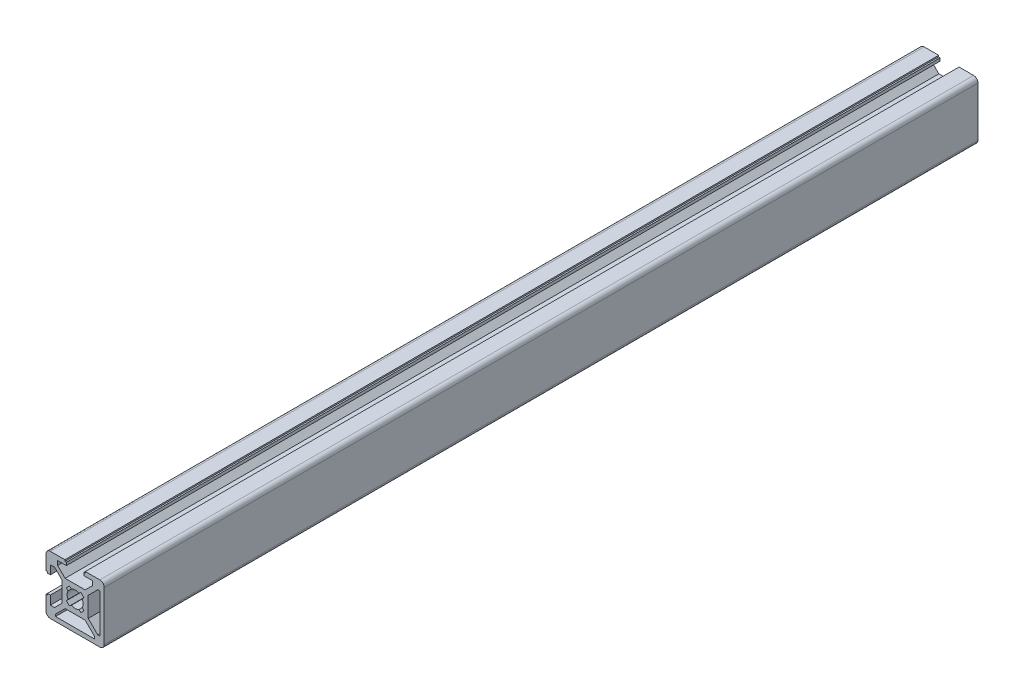
SolidWorks part; units mm, degrees
ref_plane "Front Plane" through (0, 0, 0) normal (0, 0, 1) x (1, 0, 0)
ref_plane "Top Plane" through (0, 0, 0) normal (0, 1, 0) x (1, 0, 0)
ref_plane "Right Plane" through (0, 0, 0) normal (1, 0, 0) x (0, 0, -1)
sketch "Sketch1" plane through (0, 0, 0) normal (0, 0, 1) x (1, 0, 0)
  line L1 (4.5, -3.4393) -> (4.5, 3.4393)
  line L7 (8.5, -6.7322) -> (7.7929, -6.7322)
  line L8 (7.7929, -6.7322) -> (4.5, -3.4393)
  line L9 (8.5, 6.7322) -> (8.5, -6.7322)
  line L10 (7.7929, 6.7322) -> (8.5, 6.7322)
  line L11 (4.5, 3.4393) -> (7.7929, 6.7322)
  line L21 (-2.4356, 1.2768) -> (-3.0002, 1.9496)
  line L22 (-3.0002, 1.9496) -> (-1.9496, 3.0002)
  line L23 (-1.9496, 3.0002) -> (-1.2768, 2.4356)
  line L24 (1.2768, 2.4356) -> (1.9496, 3.0002)
  line L25 (1.9496, 3.0002) -> (3.0002, 1.9496)
  line L26 (3.0002, 1.9496) -> (2.4356, 1.2768)
  line L64 (6, 7.0607) -> (3.4393, 4.5)
  line L65 (3.4393, 4.5) -> (-3.4393, 4.5)
  line L66 (-3.4393, 4.5) -> (-6, 7.0607)
  line L67 (-6, 7.0607) -> (-6, 8.5)
  line L68 (-6, 8.5) -> (-3, 8.5)
  line L69 (-3, 8.5) -> (-3, 9.5)
  line L70 (-3, 9.5) -> (-3.5, 9.5)
  line L71 (-3.5, 9.5) -> (-3.5, 10)
  line L72 (-3.5, 10) -> (-8.5, 10)
  line L73 (-10, 8.5) -> (-10, 3.5)
  line L74 (-10, 3.5) -> (-9.5, 3.5)
  line L75 (-9.5, 3.5) -> (-9.5, 3)
  line L76 (-9.5, 3) -> (-8.5, 3)
  line L77 (-8.5, 3) -> (-8.5, 6)
  line L78 (-8.5, 6) -> (-7.0607, 6)
  line L79 (-7.0607, 6) -> (-4.5, 3.4393)
  line L80 (-4.5, 3.4393) -> (-4.5, -3.4393)
  line L81 (-4.5, -3.4393) -> (-7.0607, -6)
  line L82 (-7.0607, -6) -> (-8.5, -6)
  line L83 (-8.5, -6) -> (-8.5, -3)
  line L84 (-8.5, -3) -> (-9.5, -3)
  line L85 (-9.5, -3) -> (-9.5, -3.5)
  line L86 (-9.5, -3.5) -> (-10, -3.5)
  line L87 (-10, -3.5) -> (-10, -8.5)
  line L88 (-8.5, -10) -> (8.5, -10)
  line L89 (10, -8.5) -> (10, 8.5)
  line L90 (8.5, 10) -> (3.5, 10)
  line L91 (3.5, 10) -> (3.5, 9.5)
  line L92 (3.5, 9.5) -> (3, 9.5)
  line L93 (3, 9.5) -> (3, 8.5)
  line L94 (3, 8.5) -> (6, 8.5)
  line L95 (6, 8.5) -> (6, 7.0607)
  line L97 (-1.9496, -3.0002) -> (-3.0002, -1.9496)
  line L98 (-1.2768, -2.4356) -> (-1.9496, -3.0002)
  line L99 (-3.0002, -1.9496) -> (-2.4356, -1.2768)
  line L100 (3.0002, -1.9496) -> (1.9496, -3.0002)
  line L101 (1.9496, -3.0002) -> (1.2768, -2.4356)
  line L102 (2.4356, -1.2768) -> (3.0002, -1.9496)
  line L109 (3.4393, -4.5) -> (6.7322, -7.7929)
  line L110 (6.7322, -7.7929) -> (6.7322, -8.5)
  line L111 (6.7322, -8.5) -> (-6.7322, -8.5)
  line L112 (-6.7322, -8.5) -> (-6.7322, -7.7929)
  line L113 (-3.4393, -4.5) -> (3.4393, -4.5)
  line L114 (-6.7322, -7.7929) -> (-3.4393, -4.5)
  arc A3 (1.2768, 2.4356) -> (-1.2768, 2.4356) centre (0, 0) ccw
  arc A8 (-8.5, 10) -> (-10, 8.5) centre (-8.5, 8.5) ccw
  arc A9 (-10, -8.5) -> (-8.5, -10) centre (-8.5, -8.5) ccw
  arc A10 (8.5, -10) -> (10, -8.5) centre (8.5, -8.5) ccw
  arc A11 (10, 8.5) -> (8.5, 10) centre (8.5, 8.5) ccw
  arc A15 (-1.2768, -2.4356) -> (1.2768, -2.4356) centre (0, 0) ccw
  arc A16 (2.4356, -1.2768) -> (2.4356, 1.2768) centre (0, 0) ccw
  arc A17 (-2.4356, 1.2768) -> (-2.4356, -1.2768) centre (0, 0) ccw
extrude "Boss-Extrude1" add sketch "Sketch1" along normal blind 1000
sketch "Sketch3" plane through (0, 0, 1000) normal (0, 0, 1) x (1, 0, 0)
  line L32 (6, 8.5) -> (6, 7.0607)
  line L33 (6, 7.0607) -> (3.4393, 4.5)
  line L34 (3.4393, 4.5) -> (-3.4393, 4.5)
  line L35 (-3.4393, 4.5) -> (-6, 7.0607)
  line L36 (-6, 7.0607) -> (-6, 8.5)
  line L37 (-6, 8.5) -> (-3, 8.5)
  line L38 (-3, 8.5) -> (-3, 9.5)
  line L39 (-3, 9.5) -> (-3.5, 9.5)
  line L40 (-3.5, 9.5) -> (-3.5, 10)
  line L41 (-3.5, 10) -> (-8.5, 10)
  line L42 (-10, 8.5) -> (-10, 3.5)
  line L43 (-10, 3.5) -> (-9.5, 3.5)
  line L44 (-9.5, 3.5) -> (-9.5, 3)
  line L45 (-9.5, 3) -> (-8.5, 3)
  line L46 (-8.5, 3) -> (-8.5, 6)
  line L47 (-8.5, 6) -> (-7.0607, 6)
  line L48 (-7.0607, 6) -> (-4.5, 3.4393)
  line L49 (-4.5, 3.4393) -> (-4.5, -3.4393)
  line L50 (-4.5, -3.4393) -> (-7.0607, -6)
  line L51 (-7.0607, -6) -> (-8.5, -6)
  line L52 (-8.5, -6) -> (-8.5, -3)
  line L53 (-8.5, -3) -> (-9.5, -3)
  line L54 (-9.5, -3) -> (-9.5, -3.5)
  line L55 (-9.5, -3.5) -> (-10, -3.5)
  line L56 (-10, -3.5) -> (-10, -8.5)
  line L57 (-8.5, -10) -> (8.5, -10)
  line L58 (10, -8.5) -> (10, 8.5)
  line L59 (8.5, 10) -> (3.5, 10)
  line L60 (3.5, 10) -> (3.5, 9.5)
  line L61 (3.5, 9.5) -> (3, 9.5)
  line L62 (3, 9.5) -> (3, 8.5)
  line L63 (3, 8.5) -> (6, 8.5)
  line L64 (6, 8.5) -> (6, 7.0607)
  line L65 (6, 7.0607) -> (3.4393, 4.5)
  line L66 (3.4393, 4.5) -> (-3.4393, 4.5)
  line L67 (-3.4393, 4.5) -> (-6, 7.0607)
  line L68 (-6, 7.0607) -> (-6, 8.5)
  line L69 (-6, 8.5) -> (-3, 8.5)
  line L70 (-3, 8.5) -> (-3, 9.5)
  line L71 (-3, 9.5) -> (-3.5, 9.5)
  line L72 (-3.5, 9.5) -> (-3.5, 10)
  line L73 (-3.5, 10) -> (-8.5, 10)
  line L74 (-10, 8.5) -> (-10, 3.5)
  line L75 (-10, 3.5) -> (-9.5, 3.5)
  line L76 (-9.5, 3.5) -> (-9.5, 3)
  line L77 (-9.5, 3) -> (-8.5, 3)
  line L78 (-8.5, 3) -> (-8.5, 6)
  line L79 (-8.5, 6) -> (-7.0607, 6)
  line L80 (-7.0607, 6) -> (-4.5, 3.4393)
  line L81 (-4.5, 3.4393) -> (-4.5, -3.4393)
  line L82 (-4.5, -3.4393) -> (-7.0607, -6)
  line L83 (-7.0607, -6) -> (-8.5, -6)
  line L84 (-8.5, -6) -> (-8.5, -3)
  line L85 (-8.5, -3) -> (-9.5, -3)
  line L86 (-9.5, -3) -> (-9.5, -3.5)
  line L87 (-9.5, -3.5) -> (-10, -3.5)
  line L88 (-10, -3.5) -> (-10, -8.5)
  line L89 (-8.5, -10) -> (8.5, -10)
  line L90 (10, -8.5) -> (10, 8.5)
  line L91 (8.5, 10) -> (3.5, 10)
  line L92 (3.5, 10) -> (3.5, 9.5)
  line L93 (3.5, 9.5) -> (3, 9.5)
  line L94 (3, 9.5) -> (3, 8.5)
  line L95 (3, 8.5) -> (6, 8.5)
  arc A4 (-8.5, 10) -> (-10, 8.5) centre (-8.5, 8.5) ccw
  arc A5 (-10, -8.5) -> (-8.5, -10) centre (-8.5, -8.5) ccw
  arc A6 (8.5, -10) -> (10, -8.5) centre (8.5, -8.5) ccw
  arc A7 (10, 8.5) -> (8.5, 10) centre (8.5, 8.5) ccw
  arc A8 (-8.5, 10) -> (-10, 8.5) centre (-8.5, 8.5) ccw
  arc A9 (-10, -8.5) -> (-8.5, -10) centre (-8.5, -8.5) ccw
  arc A10 (8.5, -10) -> (10, -8.5) centre (8.5, -8.5) ccw
  arc A11 (10, 8.5) -> (8.5, 10) centre (8.5, 8.5) ccw
  dimension "D1" = 0
extrude "Cut-Extrude1" cut sketch "Sketch3" against normal offset from surface (700 mm away) 300 up to face at (0, 0, 0)
sketch "Sketch4" [suppressed] plane through (0, 0, 1000) normal (0, 0, 1) x (1, 0, 0)
  line L32 (6, 8.5) -> (6, 7.0607)
  line L33 (6, 7.0607) -> (3.4393, 4.5)
  line L34 (3.4393, 4.5) -> (-3.4393, 4.5)
  line L35 (-3.4393, 4.5) -> (-6, 7.0607)
  line L36 (-6, 7.0607) -> (-6, 8.5)
  line L37 (-6, 8.5) -> (-3, 8.5)
  line L38 (-3, 8.5) -> (-3, 9.5)
  line L39 (-3, 9.5) -> (-3.5, 9.5)
  line L40 (-3.5, 9.5) -> (-3.5, 10)
  line L41 (-3.5, 10) -> (-8.5, 10)
  line L42 (-10, 8.5) -> (-10, 3.5)
  line L43 (-10, 3.5) -> (-9.5, 3.5)
  line L44 (-9.5, 3.5) -> (-9.5, 3)
  line L45 (-9.5, 3) -> (-8.5, 3)
  line L46 (-8.5, 3) -> (-8.5, 6)
  line L47 (-8.5, 6) -> (-7.0607, 6)
  line L48 (-7.0607, 6) -> (-4.5, 3.4393)
  line L49 (-4.5, 3.4393) -> (-4.5, -3.4393)
  line L50 (-4.5, -3.4393) -> (-7.0607, -6)
  line L51 (-7.0607, -6) -> (-8.5, -6)
  line L52 (-8.5, -6) -> (-8.5, -3)
  line L53 (-8.5, -3) -> (-9.5, -3)
  line L54 (-9.5, -3) -> (-9.5, -3.5)
  line L55 (-9.5, -3.5) -> (-10, -3.5)
  line L56 (-10, -3.5) -> (-10, -8.5)
  line L57 (-8.5, -10) -> (8.5, -10)
  line L58 (10, -8.5) -> (10, 8.5)
  line L59 (8.5, 10) -> (3.5, 10)
  line L60 (3.5, 10) -> (3.5, 9.5)
  line L61 (3.5, 9.5) -> (3, 9.5)
  line L62 (3, 9.5) -> (3, 8.5)
  line L63 (3, 8.5) -> (6, 8.5)
  line L64 (6, 8.5) -> (6, 7.0607)
  line L65 (6, 7.0607) -> (3.4393, 4.5)
  line L66 (3.4393, 4.5) -> (-3.4393, 4.5)
  line L67 (-3.4393, 4.5) -> (-6, 7.0607)
  line L68 (-6, 7.0607) -> (-6, 8.5)
  line L69 (-6, 8.5) -> (-3, 8.5)
  line L70 (-3, 8.5) -> (-3, 9.5)
  line L71 (-3, 9.5) -> (-3.5, 9.5)
  line L72 (-3.5, 9.5) -> (-3.5, 10)
  line L73 (-3.5, 10) -> (-8.5, 10)
  line L74 (-10, 8.5) -> (-10, 3.5)
  line L75 (-10, 3.5) -> (-9.5, 3.5)
  line L76 (-9.5, 3.5) -> (-9.5, 3)
  line L77 (-9.5, 3) -> (-8.5, 3)
  line L78 (-8.5, 3) -> (-8.5, 6)
  line L79 (-8.5, 6) -> (-7.0607, 6)
  line L80 (-7.0607, 6) -> (-4.5, 3.4393)
  line L81 (-4.5, 3.4393) -> (-4.5, -3.4393)
  line L82 (-4.5, -3.4393) -> (-7.0607, -6)
  line L83 (-7.0607, -6) -> (-8.5, -6)
  line L84 (-8.5, -6) -> (-8.5, -3)
  line L85 (-8.5, -3) -> (-9.5, -3)
  line L86 (-9.5, -3) -> (-9.5, -3.5)
  line L87 (-9.5, -3.5) -> (-10, -3.5)
  line L88 (-10, -3.5) -> (-10, -8.5)
  line L89 (-8.5, -10) -> (8.5, -10)
  line L90 (10, -8.5) -> (10, 8.5)
  line L91 (8.5, 10) -> (3.5, 10)
  line L92 (3.5, 10) -> (3.5, 9.5)
  line L93 (3.5, 9.5) -> (3, 9.5)
  line L94 (3, 9.5) -> (3, 8.5)
  line L95 (3, 8.5) -> (6, 8.5)
  arc A4 (-8.5, 10) -> (-10, 8.5) centre (-8.5, 8.5) ccw
  arc A5 (-10, -8.5) -> (-8.5, -10) centre (-8.5, -8.5) ccw
  arc A6 (8.5, -10) -> (10, -8.5) centre (8.5, -8.5) ccw
  arc A7 (10, 8.5) -> (8.5, 10) centre (8.5, 8.5) ccw
  arc A8 (-8.5, 10) -> (-10, 8.5) centre (-8.5, 8.5) ccw
  arc A9 (-10, -8.5) -> (-8.5, -10) centre (-8.5, -8.5) ccw
  arc A10 (8.5, -10) -> (10, -8.5) centre (8.5, -8.5) ccw
  arc A11 (10, 8.5) -> (8.5, 10) centre (8.5, 8.5) ccw
  dimension "D1" = 0
extrude "Cut-Extrude2" [suppressed] cut sketch "Sketch4" against normal offset from surface (540 mm away) 500
sketch "Sketch5" [suppressed] plane through (0, 0, 0) normal (0, 0, -1) x (-1, 0, 0)
  line L32 (-6, 7.0607) -> (-6, 8.5)
  line L33 (-6, 8.5) -> (-3, 8.5)
  line L34 (-3, 8.5) -> (-3, 9.5)
  line L35 (-3, 9.5) -> (-3.5, 9.5)
  line L36 (-3.5, 9.5) -> (-3.5, 10)
  line L37 (-3.5, 10) -> (-8.5, 10)
  line L38 (-10, 8.5) -> (-10, -8.5)
  line L39 (-8.5, -10) -> (8.5, -10)
  line L40 (10, -8.5) -> (10, -3.5)
  line L41 (10, -3.5) -> (9.5, -3.5)
  line L42 (9.5, -3.5) -> (9.5, -3)
  line L43 (9.5, -3) -> (8.5, -3)
  line L44 (8.5, -3) -> (8.5, -6)
  line L45 (8.5, -6) -> (7.0607, -6)
  line L46 (7.0607, -6) -> (4.5, -3.4393)
  line L47 (4.5, -3.4393) -> (4.5, 3.4393)
  line L48 (4.5, 3.4393) -> (7.0607, 6)
  line L49 (7.0607, 6) -> (8.5, 6)
  line L50 (8.5, 6) -> (8.5, 3)
  line L51 (8.5, 3) -> (9.5, 3)
  line L52 (9.5, 3) -> (9.5, 3.5)
  line L53 (9.5, 3.5) -> (10, 3.5)
  line L54 (10, 3.5) -> (10, 8.5)
  line L55 (8.5, 10) -> (3.5, 10)
  line L56 (3.5, 10) -> (3.5, 9.5)
  line L57 (3.5, 9.5) -> (3, 9.5)
  line L58 (3, 9.5) -> (3, 8.5)
  line L59 (3, 8.5) -> (6, 8.5)
  line L60 (6, 8.5) -> (6, 7.0607)
  line L61 (6, 7.0607) -> (3.4393, 4.5)
  line L62 (3.4393, 4.5) -> (-3.4393, 4.5)
  line L63 (-3.4393, 4.5) -> (-6, 7.0607)
  line L64 (-6, 7.0607) -> (-6, 8.5)
  line L65 (-6, 8.5) -> (-3, 8.5)
  line L66 (-3, 8.5) -> (-3, 9.5)
  line L67 (-3, 9.5) -> (-3.5, 9.5)
  line L68 (-3.5, 9.5) -> (-3.5, 10)
  line L69 (-3.5, 10) -> (-8.5, 10)
  line L70 (-10, 8.5) -> (-10, -8.5)
  line L71 (-8.5, -10) -> (8.5, -10)
  line L72 (10, -8.5) -> (10, -3.5)
  line L73 (10, -3.5) -> (9.5, -3.5)
  line L74 (9.5, -3.5) -> (9.5, -3)
  line L75 (9.5, -3) -> (8.5, -3)
  line L76 (8.5, -3) -> (8.5, -6)
  line L77 (8.5, -6) -> (7.0607, -6)
  line L78 (7.0607, -6) -> (4.5, -3.4393)
  line L79 (4.5, -3.4393) -> (4.5, 3.4393)
  line L80 (4.5, 3.4393) -> (7.0607, 6)
  line L81 (7.0607, 6) -> (8.5, 6)
  line L82 (8.5, 6) -> (8.5, 3)
  line L83 (8.5, 3) -> (9.5, 3)
  line L84 (9.5, 3) -> (9.5, 3.5)
  line L85 (9.5, 3.5) -> (10, 3.5)
  line L86 (10, 3.5) -> (10, 8.5)
  line L87 (8.5, 10) -> (3.5, 10)
  line L88 (3.5, 10) -> (3.5, 9.5)
  line L89 (3.5, 9.5) -> (3, 9.5)
  line L90 (3, 9.5) -> (3, 8.5)
  line L91 (3, 8.5) -> (6, 8.5)
  line L92 (6, 8.5) -> (6, 7.0607)
  line L93 (6, 7.0607) -> (3.4393, 4.5)
  line L94 (3.4393, 4.5) -> (-3.4393, 4.5)
  line L95 (-3.4393, 4.5) -> (-6, 7.0607)
  arc A4 (-8.5, 10) -> (-10, 8.5) centre (-8.5, 8.5) ccw
  arc A5 (-10, -8.5) -> (-8.5, -10) centre (-8.5, -8.5) ccw
  arc A6 (8.5, -10) -> (10, -8.5) centre (8.5, -8.5) ccw
  arc A7 (10, 8.5) -> (8.5, 10) centre (8.5, 8.5) ccw
  arc A8 (-8.5, 10) -> (-10, 8.5) centre (-8.5, 8.5) ccw
  arc A9 (-10, -8.5) -> (-8.5, -10) centre (-8.5, -8.5) ccw
  arc A10 (8.5, -10) -> (10, -8.5) centre (8.5, -8.5) ccw
  arc A11 (10, 8.5) -> (8.5, 10) centre (8.5, 8.5) ccw
  dimension "D1" = 0
extrude "Cut-Extrude3" [suppressed] cut sketch "Sketch5" against normal offset from surface (800 mm away) 190
